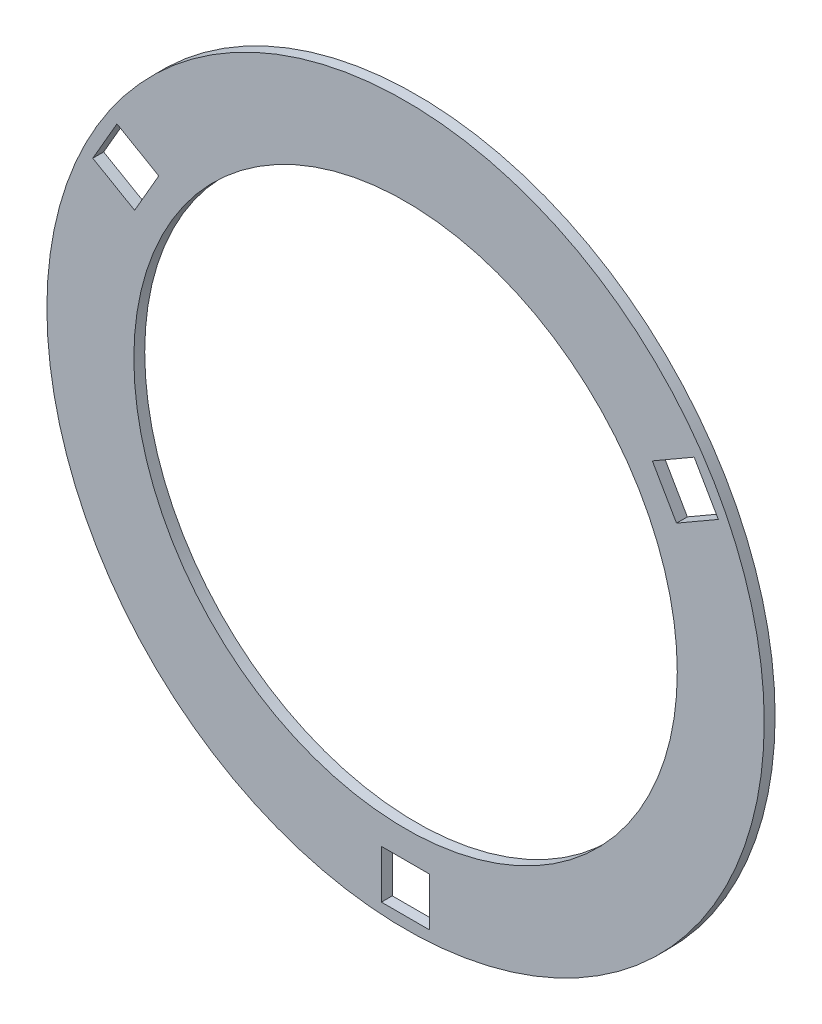
SolidWorks part; units mm, degrees
ref_plane "Front Plane" through (0, 0, 0) normal (0, 0, 1) x (1, 0, 0)
ref_plane "Top Plane" through (0, 0, 0) normal (0, 1, 0) x (1, 0, 0)
ref_plane "Right Plane" through (0, 0, 0) normal (1, 0, 0) x (0, 0, -1)
sketch "Sketch2" plane through (0, 0, 0) normal (0, 0, 1) x (1, 0, 0)
  line L0 (-272.7968, 133.9204) -> (-295.0218, 95.4256)
  line L1 (-295.0218, 95.4256) -> (-256.527, 73.2006)
  line L2 (-256.527, 73.2006) -> (-234.302, 111.6954)
  line L3 (-234.302, 111.6954) -> (-272.7968, 133.9204)
  line L4 (258.2818, 133.9204) -> (219.787, 111.6954)
  line L5 (219.787, 111.6954) -> (242.012, 73.2006)
  line L6 (242.012, 73.2006) -> (280.5068, 95.4256)
  line L7 (280.5068, 95.4256) -> (258.2818, 133.9204)
  line L8 (-29.4825, -320.052) -> (-29.4825, -364.502)
  line L9 (-29.4825, -364.502) -> (14.9675, -364.502)
  line L10 (14.9675, -364.502) -> (14.9675, -320.052)
  line L11 (14.9675, -320.052) -> (-29.4825, -320.052)
  circle A0 centre (-7.2575, -45.052) radius 330
  arc A1 (-277.6485, -251.1799) -> (-277.6485, 161.0759) centre (-7.2575, -45.052) ccw construction
  circle A2 centre (-7.2575, -45.052) radius 250
  arc A3 (220.9978, -147.0301) -> (18.5545, 203.6119) centre (-7.2575, -45.052) ccw construction
  dimension "D1" = 660
extrude "Boss-Extrude1" add sketch "Sketch2" along normal blind 10
